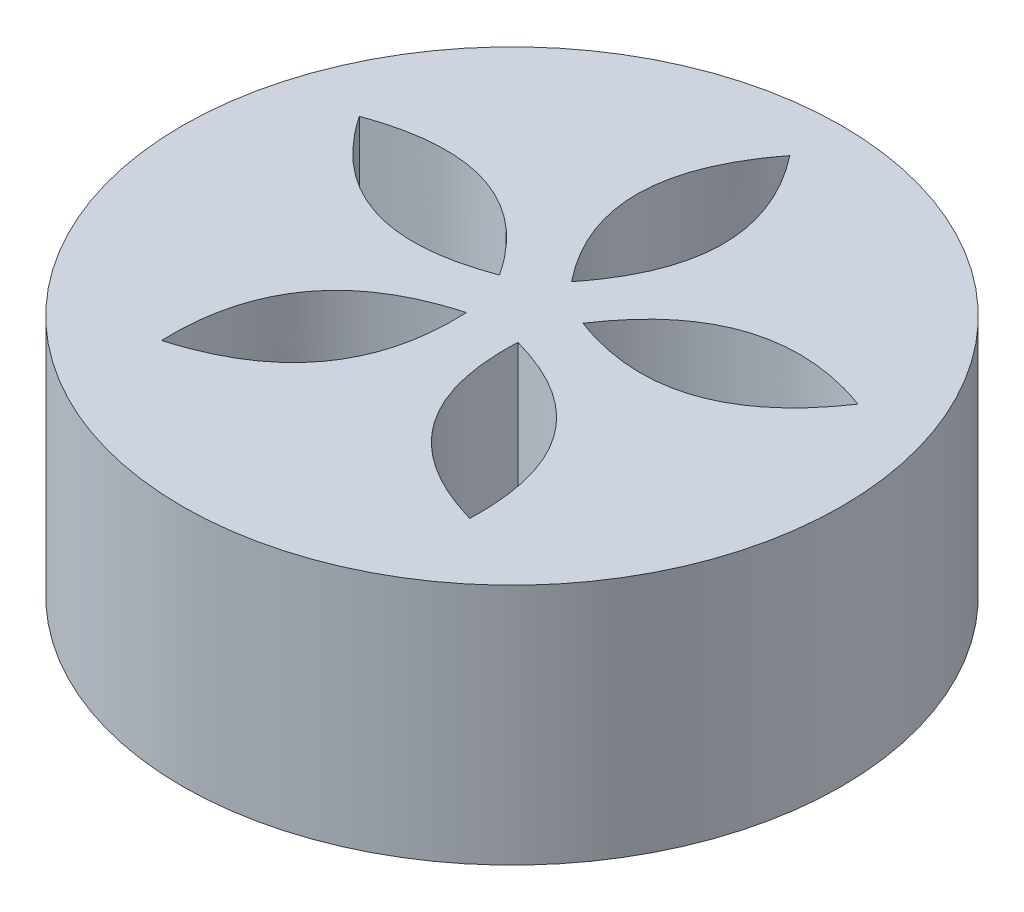
SolidWorks part; units mm, degrees
ref_plane "前视基准面" through (0, 0, 0) normal (0, 0, 1) x (1, 0, 0)
ref_plane "上视基准面" through (0, 0, 0) normal (0, 1, 0) x (1, 0, 0)
ref_plane "右视基准面" through (0, 0, 0) normal (1, 0, 0) x (0, 0, -1)
sketch "草图1" plane through (0, 0, 0) normal (0, 1, 0) x (1, 0, 0)
  circle A0 centre (0, 0) radius 34
  dimension "D1" = 68
extrude "凸台-拉伸1" add sketch "草图1" along normal blind 25
sketch "草图2" plane through (0, 0, 0) normal (0, -1, 0) x (1, 0, 0)
  line L0 (0, -1.617) -> (0, -32.6372) construction
  spline S0 degree 2 poles (0, -6.1427) (8.8922, -17.2527) (0, -28.654) knots 0 0 0 1 1 1
  spline S1 degree 2 poles (0, -6.1427) (-8.8922, -17.2527) (0, -28.654) knots 0 0 0 1 1 1
  spline S2 degree 2 poles (-4.3042, -3.0155) (-17.6183, 2.0083) (-25.7137, -9.9719) knots 0 0 0 1 1 1
  spline S3 degree 2 poles (-4.3042, -3.0155) (-12.1226, -14.9057) (-25.7137, -9.9719) knots 0 0 0 1 1 1
  spline S4 degree 2 poles (-2.6601, 2.0443) (-1.9965, 16.2592) (-15.8919, 20.2564) knots 0 0 0 1 1 1
  spline S5 degree 2 poles (-2.6601, 2.0443) (-16.3844, 5.8058) (-15.8919, 20.2564) knots 0 0 0 1 1 1
  spline S6 degree 2 poles (2.6601, 2.0443) (16.3844, 5.8058) (15.8919, 20.2564) knots 0 0 0 1 1 1
  spline S7 degree 2 poles (2.6601, 2.0443) (1.9965, 16.2592) (15.8919, 20.2564) knots 0 0 0 1 1 1
  spline S8 degree 2 poles (4.3042, -3.0155) (12.1226, -14.9057) (25.7137, -9.9719) knots 0 0 0 1 1 1
  spline S9 degree 2 poles (4.3042, -3.0155) (17.6183, 2.0083) (25.7137, -9.9719) knots 0 0 0 1 1 1
  point P25 (0, -1.617)
  point P26 (0, -1.617)
extrude "切除-拉伸1" cut sketch "草图2" against normal blind 25
